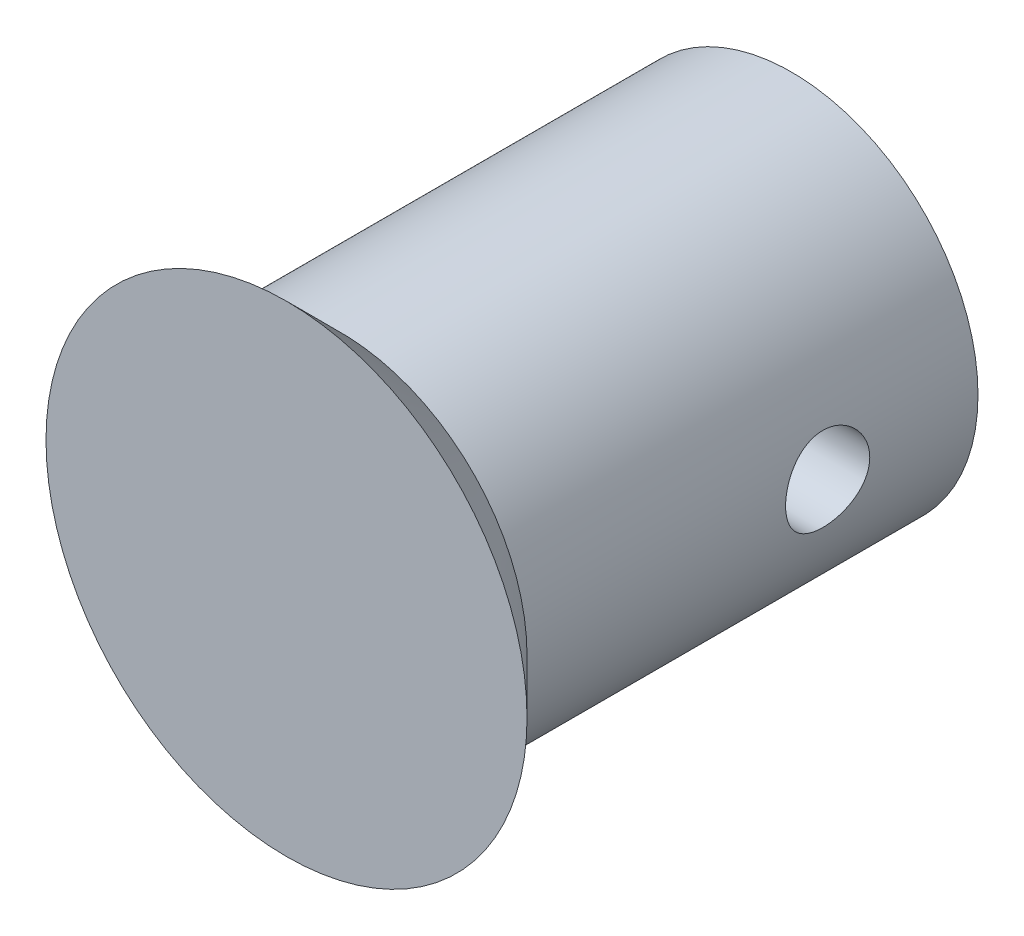
SolidWorks part; units mm, degrees
material "AISI 1020"
ref_plane "Спереди" through (0, 0, 0) normal (0, 0, 1) x (1, 0, 0)
ref_plane "Сверху" through (0, 0, 0) normal (0, 1, 0) x (1, 0, 0)
ref_plane "Справа" through (0, 0, 0) normal (1, 0, 0) x (0, 0, -1)
sketch "Эскиз1" plane through (0, 0, 0) normal (1, 0, 0) x (0, 0, -1)
  line L0 (-1000, 0) -> (49000, 0) construction
  line L1 (0, 0) -> (0, 10)
  line L2 (0, 10) -> (2.25, 7.75)
  line L3 (2.25, 7.75) -> (21, 7.75)
  line L4 (21, 7.75) -> (21, 0)
  line L5 (21, 0) -> (0, 0)
  line L6 (4, 8) -> (2, 8) construction
  line L7 (2, 8) -> (0, 10) construction
  line L8 (13, -16) -> (13, 16) construction
  point P15 (21, 3.875)
  dimension "D1" = 0.25
  dimension "D2" = 8
revolve "Повернуть1" add sketch "Эскиз1" angle 360 about L0
sketch "Эскиз2" plane through (0, 0, 0) normal (1, 0, 0) x (0, 0, -1)
  circle A0 centre (14.75, 0) radius 1.75
  dimension "D1" = 3.5
extrude "Вырез-Вытянуть1" cut sketch "Эскиз2" against normal through all both and the other way through all
